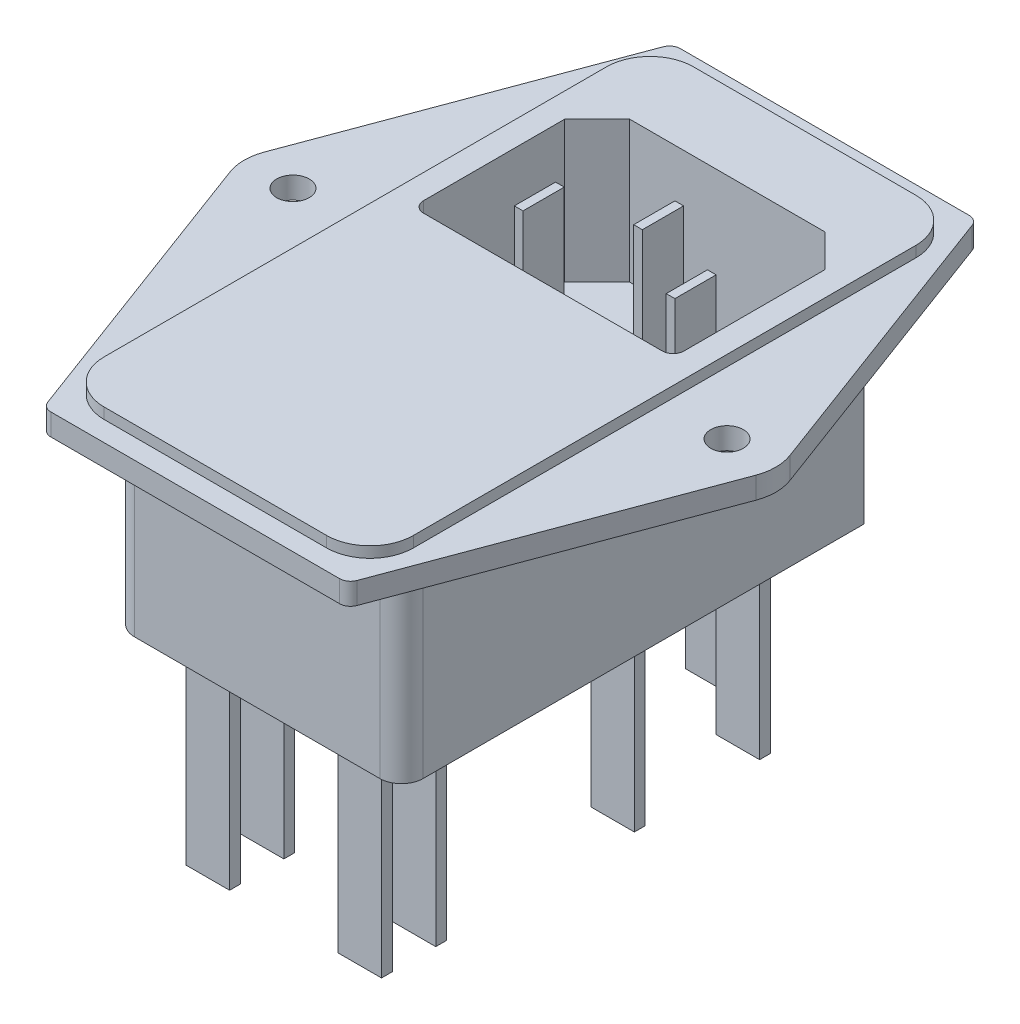
SolidWorks part; units mm, degrees
ref_plane "前视基准面" through (0, 0, 0) normal (0, 0, 1) x (1, 0, 0)
ref_plane "上视基准面" through (0, 0, 0) normal (0, 1, 0) x (1, 0, 0)
ref_plane "右视基准面" through (0, 0, 0) normal (1, 0, 0) x (0, 0, -1)
sketch "草图1" plane through (0, 0, 0) normal (0, 1, 0) x (1, 0, 0)
  line L0 (0, 0) -> (50000, 0) construction
  line L1 (0, 0) -> (0, 50000) construction
  line L2 (-24.217, 1.5708) -> (-14.2425, 28.3491)
  line L3 (-13.3054, 29) -> (13.3054, 29)
  line L5 (-13.3054, -29) -> (13.3054, -29)
  line L7 (-24.217, -1.5708) -> (-14.2425, -28.3491)
  line L8 (24.217, -1.5708) -> (14.2425, -28.3491)
  line L9 (24.217, 1.5708) -> (14.2425, 28.3491)
  circle A0 centre (-20, 0) radius 1.5
  arc A1 (-24.217, 1.5708) -> (-24.217, -1.5708) centre (-20, 0) ccw
  circle A2 centre (20, 0) radius 1.5
  arc A3 (24.217, 1.5708) -> (24.217, -1.5708) centre (20, 0) cw
  arc A4 (13.3054, -29) -> (14.2425, -28.3491) centre (13.3054, -28) ccw
  arc A5 (-14.2425, -28.3491) -> (-13.3054, -29) centre (-13.3054, -28) ccw
  arc A6 (-13.3054, 29) -> (-14.2425, 28.3491) centre (-13.3054, 28) ccw
  arc A7 (13.3054, 29) -> (14.2425, 28.3491) centre (13.3054, 28) cw
  point P19 (14, -29)
  point P22 (-14, -29)
  point P25 (-14, 29)
  point P28 (14, 29)
  dimension "D1" = 3
  dimension "D3" = 28
  dimension "D5" = 1
  dimension "D2" = 20
  dimension "D4" = 58
extrude "凸台-拉伸1" add sketch "草图1" along normal blind 2
sketch "草图2" plane through (0, 0, 0) normal (0, -1, 0) x (1, 0, 0)
  line L0 (0, 0) -> (50000, 0) construction
  line L1 (0, 0) -> (0, 50000) construction
  line L2 (-13.3, -19.3) -> (-9.3, -23.3)
  line L3 (-11.3, 23.3) -> (11.3, 23.3)
  line L4 (-13.3, 21.3) -> (-13.3, -19.3)
  line L5 (-9.3, -23.3) -> (9.3, -23.3)
  line L6 (13.3, 21.3) -> (13.3, -19.3)
  line L7 (9.3, -23.3) -> (13.3, -19.3)
  arc A0 (11.3, 23.3) -> (13.3, 21.3) centre (11.3, 21.3) cw
  arc A1 (-11.3, 23.3) -> (-13.3, 21.3) centre (-11.3, 21.3) ccw
  point P6 (13.3, -23.3)
  point P7 (-13.3, -23.3)
  point P11 (13.3, 23.3)
  point P14 (-13.3, 23.3)
  dimension "D3" = 2
  dimension "D1" = 26.6
  dimension "D2" = 46.6
extrude "凸台-拉伸2" add sketch "草图2" along normal blind 17.8
sketch "草图4" plane through (0, 2, 0) normal (0, 1, 0) x (1, 0, 0)
  line L0 (0, 0) -> (50000, 0) construction
  line L1 (0, 0) -> (0, 50000) construction
  line L3 (-10.25, 27.15) -> (10.25, 27.15)
  line L4 (-14.25, 23.15) -> (-14.25, -23.15)
  line L5 (-10.25, -27.15) -> (10.25, -27.15)
  line L6 (14.25, 23.15) -> (14.25, -23.15)
  arc A0 (-14.25, -23.15) -> (-10.25, -27.15) centre (-10.25, -23.15) ccw
  arc A1 (10.25, -27.15) -> (14.25, -23.15) centre (10.25, -23.15) ccw
  arc A2 (10.25, 27.15) -> (14.25, 23.15) centre (10.25, 23.15) cw
  arc A3 (-10.25, 27.15) -> (-14.25, 23.15) centre (-10.25, 23.15) ccw
  point P11 (-14.25, -27.15)
  point P14 (14.25, -27.15)
  point P17 (14.25, 27.15)
  dimension "D3" = 4
  dimension "D1" = 54.3
  dimension "D2" = 28.5
extrude "凸台-拉伸3" add sketch "草图4" along normal blind 1
sketch "草图3" plane through (0, 2, 0) normal (0, 1, 0) x (1, 0, 0)
  line L0 (0, 0) -> (0, 50000) construction
  line L1 (-9, 20.0343) -> (9, 20.0343)
  line L2 (-12, 17.0343) -> (-12, 4.0343)
  line L3 (-11, 3.0343) -> (11, 3.0343)
  line L4 (12, 17.0343) -> (12, 4.0343)
  line L5 (-12, 17.0343) -> (-9, 20.0343)
  line L6 (9, 20.0343) -> (12, 17.0343)
  arc A0 (11, 3.0343) -> (12, 4.0343) centre (11, 4.0343) ccw
  arc A1 (-12, 4.0343) -> (-11, 3.0343) centre (-11, 4.0343) ccw
  point P0 (-12, 20.0343)
  point P3 (12, 20.0343)
  point P9 (12, 3.0343)
  dimension "D3" = 1
  dimension "D1" = 24
  dimension "D2" = 17
extrude "切除-拉伸1" cut sketch "草图3" against normal blind 13 from surface at 1 starting at face at (0, 3, 0)
sketch "草图5" plane through (0, -10, 0) normal (0, 1, 0) x (1, 0, 0)
  line L0 (0, -1.1409) -> (0, 49998.8591) construction
  line L1 (-7.4, 11.598) -> (-6.6, 11.598)
  line L2 (-0.4, 15.598) -> (0.4, 15.598)
  line L3 (-0.4, 15.598) -> (-0.4, 11.798)
  line L4 (-0.4, 11.798) -> (0.4, 11.798)
  line L5 (0.4, 15.598) -> (0.4, 11.798)
  line L6 (-7.4, 11.598) -> (-7.4, 7.798)
  line L7 (-7.4, 7.798) -> (-6.6, 7.798)
  line L8 (-6.6, 11.598) -> (-6.6, 7.798)
  line L9 (6.6, 11.598) -> (7.4, 11.598)
  line L10 (6.6, 11.598) -> (6.6, 7.798)
  line L11 (6.6, 7.798) -> (7.4, 7.798)
  line L12 (7.4, 11.598) -> (7.4, 7.798)
  line L17 (-0.4, 11.598) -> (0.4, 11.598) [skipped]
  line L18 (-0.4, 11.598) -> (-0.4, 7.798) [skipped]
  line L19 (-0.4, 7.798) -> (0.4, 7.798) [skipped]
  line L20 (0.4, 11.598) -> (0.4, 7.798) [skipped]
  line L21 (6.6, 15.598) -> (7.4, 15.598) [skipped]
  line L22 (6.6, 15.598) -> (6.6, 11.798) [skipped]
  line L23 (6.6, 11.798) -> (7.4, 11.798) [skipped]
  line L24 (7.4, 15.598) -> (7.4, 11.798) [skipped]
  dimension "D1" = 3.8
  dimension "D2" = 0.8
  dimension "D3" = 2
  dimension "D4" = 2
  dimension "D5" = 2
extrude "凸台-拉伸4" add sketch "草图5" along normal blind 13
sketch "草图6" plane through (0, -17.8, 0) normal (0, -1, 0) x (1, 0, 0)
  line L1 (9.3, 21.1399) -> (5.3, 21.1399)
  line L2 (9.3, 21.1399) -> (9.3, 20.1399)
  line L3 (9.3, 20.1399) -> (5.3, 20.1399)
  line L4 (5.3, 21.1399) -> (5.3, 20.1399)
  line L5 (9.3, 21.1399) -> (5.3, 20.1399) construction
  line L6 (9.3, 20.1399) -> (5.3, 21.1399) construction
  line L7 (-4.7, 21.1399) -> (-8.7, 21.1399)
  line L8 (-4.7, 21.1399) -> (-4.7, 20.1399)
  line L9 (-4.7, 20.1399) -> (-8.7, 20.1399)
  line L10 (-8.7, 21.1399) -> (-8.7, 20.1399)
  line L11 (-4.7, 21.1399) -> (-8.7, 20.1399) construction
  line L12 (-4.7, 20.1399) -> (-8.7, 21.1399) construction
  line L13 (9.3, 16.1399) -> (5.3, 16.1399)
  line L14 (9.3, 16.1399) -> (9.3, 15.1399)
  line L15 (9.3, 15.1399) -> (5.3, 15.1399)
  line L16 (5.3, 16.1399) -> (5.3, 15.1399)
  line L17 (9.3, 16.1399) -> (5.3, 15.1399) construction
  line L18 (9.3, 15.1399) -> (5.3, 16.1399) construction
  line L19 (-4.7, 16.1399) -> (-8.7, 16.1399)
  line L20 (-4.7, 16.1399) -> (-4.7, 15.1399)
  line L21 (-4.7, 15.1399) -> (-8.7, 15.1399)
  line L22 (-8.7, 16.1399) -> (-8.7, 15.1399)
  line L23 (-4.7, 16.1399) -> (-8.7, 15.1399) construction
  line L24 (-4.7, 15.1399) -> (-8.7, 16.1399) construction
  line L25 (9.3, -2.1595) -> (5.3, -2.1595)
  line L26 (9.3, -2.1595) -> (9.3, -3.1595)
  line L27 (9.3, -3.1595) -> (5.3, -3.1595)
  line L28 (5.3, -2.1595) -> (5.3, -3.1595)
  line L29 (9.3, -2.1595) -> (5.3, -3.1595) construction
  line L30 (9.3, -3.1595) -> (5.3, -2.1595) construction
  line L31 (9.3, -13.7027) -> (5.3, -13.7027)
  line L32 (9.3, -13.7027) -> (9.3, -14.7027)
  line L33 (9.3, -14.7027) -> (5.3, -14.7027)
  line L34 (5.3, -13.7027) -> (5.3, -14.7027)
  line L35 (9.3, -13.7027) -> (5.3, -14.7027) construction
  line L36 (9.3, -14.7027) -> (5.3, -13.7027) construction
  line L37 (2.6344, -17.5474) -> (-1.3656, -17.5474)
  line L38 (2.6344, -17.5474) -> (2.6344, -18.5474)
  line L39 (2.6344, -18.5474) -> (-1.3656, -18.5474)
  line L40 (-1.3656, -17.5474) -> (-1.3656, -18.5474)
  line L41 (2.6344, -17.5474) -> (-1.3656, -18.5474) construction
  line L42 (2.6344, -18.5474) -> (-1.3656, -17.5474) construction
  line L43 (13.3, -19.3) -> (13.3, 21.3) construction
  point P0 (7.3, 20.6399)
  point P5 (-6.7, 20.6399)
  point P10 (7.3, 15.6399)
  point P15 (-6.7, 15.6399)
  point P20 (7.3, -2.6595)
  point P25 (7.3, -14.2027)
  point P30 (0.6344, -18.0474)
  dimension "D1" = 4
  dimension "D2" = 4
  dimension "D3" = 1
  dimension "D4" = 4
  dimension "D5" = 10
extrude "凸台-拉伸5" add sketch "草图6" along normal blind 18
